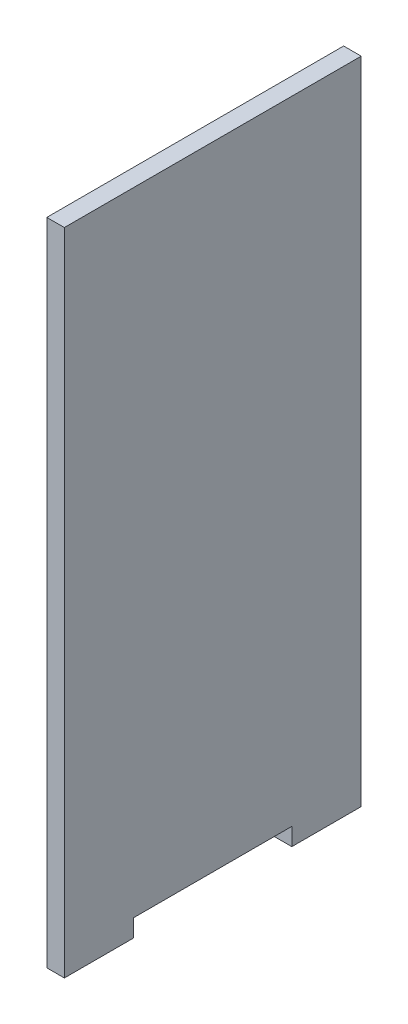
SolidWorks part; units mm, degrees
ref_plane "Front Plane" through (0, 0, 0) normal (0, 0, 1) x (1, 0, 0)
ref_plane "Top Plane" through (0, 0, 0) normal (0, 1, 0) x (1, 0, 0)
ref_plane "Right Plane" through (0, 0, 0) normal (1, 0, 0) x (0, 0, -1)
sketch "Sketch1" plane through (0, 0, 0) normal (1, 0, 0) x (0, 0, -1)
  line L0 (0, 227.7876) -> (0, -115.1881) construction
  line L1 (-42.25, 180) -> (42.25, 180)
  line L2 (-42.25, 180) -> (-42.25, 0)
  line L3 (-22.5, 0) -> (22.5, 0)
  line L4 (42.25, 180) -> (42.25, 0)
  line L5 (-42.25, 0) -> (-42.25, -5)
  line L6 (-42.25, -5) -> (-22.5, -5)
  line L7 (-22.5, -5) -> (-22.5, 0)
  line L8 (42.25, 0) -> (42.25, -5)
  line L9 (22.5, -5) -> (22.5, 0)
  line L10 (42.25, -5) -> (22.5, -5)
  line L11 (-42.25, 0) -> (-22.5, 0) construction
  line L12 (22.5, 0) -> (42.25, 0) construction
  dimension "D1" = 180
  dimension "D2" = 84.5
  dimension "D3" = 5
  dimension "D4" = 19.75
  dimension "D5" = 45
extrude "Boss-Extrude1" add sketch "Sketch1" along normal blind 5
